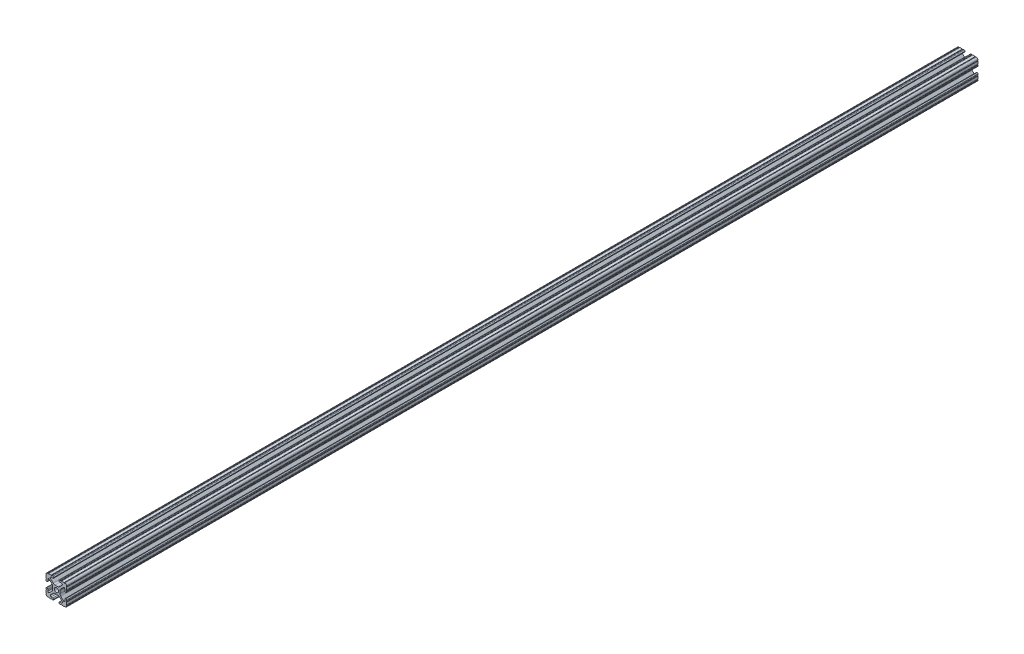
SolidWorks part; units mm, degrees
ref_plane "Front Plane" through (0, 0, 0) normal (0, 0, 1) x (1, 0, 0)
ref_plane "Top Plane" through (0, 0, 0) normal (0, 1, 0) x (1, 0, 0)
ref_plane "Right Plane" through (0, 0, 0) normal (1, 0, 0) x (0, 0, -1)
sketch "Sketch1" plane through (0, 0, 0) normal (0, 0, 1) x (1, 0, 0)
  line L88 (-7.1797, -8.6452) -> (-3.9523, -5.4237)
  line L89 (-1.7093, -4.4958) -> (1.7093, -4.4958)
  line L90 (3.9523, -5.4237) -> (7.1797, -8.6452)
  line L91 (6.4164, -10.4902) -> (4.2875, -10.4902)
  line L92 (3.2385, -11.5392) -> (3.2385, -11.651)
  line L93 (4.2875, -12.7) -> (5.3171, -12.7)
  line L94 (6.3331, -12.7) -> (9.5504, -12.7)
  line L95 (12.7, -9.5504) -> (12.7, -6.3331)
  line L96 (12.7, -5.3171) -> (12.7, -4.2875)
  line L97 (11.651, -3.2385) -> (11.5392, -3.2385)
  line L98 (10.4902, -4.2875) -> (10.4902, -6.4021)
  line L99 (8.7371, -7.1294) -> (5.441, -3.8408)
  line L100 (4.5085, -1.5932) -> (4.5085, 1.5932)
  line L101 (5.441, 3.8408) -> (8.7371, 7.1294)
  line L102 (10.4902, 6.4021) -> (10.4902, 4.2875)
  line L103 (11.5392, 3.2385) -> (11.651, 3.2385)
  line L104 (12.7, 4.2875) -> (12.7, 5.3171)
  line L105 (12.7, 6.3331) -> (12.7, 9.5504)
  line L106 (9.5504, 12.7) -> (6.3331, 12.7)
  line L107 (5.3171, 12.7) -> (4.2875, 12.7)
  line L108 (3.2385, 11.651) -> (3.2385, 11.5392)
  line L109 (4.2875, 10.4902) -> (6.4768, 10.4902)
  line L110 (7.207, 8.7244) -> (3.8983, 5.4232)
  line L111 (1.6558, 4.4958) -> (-1.6558, 4.4958)
  line L112 (-3.8983, 5.4232) -> (-7.207, 8.7244)
  line L113 (-6.4768, 10.4902) -> (-4.2875, 10.4902)
  line L114 (-3.2385, 11.5392) -> (-3.2385, 11.651)
  line L115 (-4.2875, 12.7) -> (-5.3171, 12.7)
  line L116 (-6.3331, 12.7) -> (-9.5504, 12.7)
  line L117 (-12.7, 9.5504) -> (-12.7, 6.3331)
  line L118 (-12.7, 5.3171) -> (-12.7, 4.2875)
  line L119 (-11.651, 3.2385) -> (-11.5392, 3.2385)
  line L120 (-10.4902, 4.2875) -> (-10.4902, 6.4021)
  line L121 (-8.7371, 7.1294) -> (-5.441, 3.8408)
  line L122 (-4.5085, 1.5932) -> (-4.5085, -1.5932)
  line L123 (-5.441, -3.8408) -> (-8.7371, -7.1294)
  line L124 (-10.4902, -6.4021) -> (-10.4902, -4.2875)
  line L125 (-11.5392, -3.2385) -> (-11.651, -3.2385)
  line L126 (-12.7, -4.2875) -> (-12.7, -5.3171)
  line L127 (-12.7, -6.3331) -> (-12.7, -9.5504)
  line L128 (-9.5504, -12.7) -> (-6.3331, -12.7)
  line L129 (-5.3171, -12.7) -> (-4.2875, -12.7)
  line L130 (-3.2385, -11.651) -> (-3.2385, -11.5392)
  line L131 (-4.2875, -10.4902) -> (-6.4164, -10.4902)
  circle A1 centre (0, 0) radius 2.6035
  arc A104 (-7.1797, -8.6452) -> (-6.4164, -10.4902) centre (-6.4164, -9.4098) ccw
  arc A105 (-1.7093, -4.4958) -> (-3.9523, -5.4237) centre (-1.7093, -7.6708) ccw
  arc A106 (3.9523, -5.4237) -> (1.7093, -4.4958) centre (1.7093, -7.6708) ccw
  arc A107 (6.4164, -10.4902) -> (7.1797, -8.6452) centre (6.4164, -9.4098) ccw
  arc A108 (4.2875, -10.4902) -> (3.2385, -11.5392) centre (4.2875, -11.5392) ccw
  arc A109 (3.2385, -11.651) -> (4.2875, -12.7) centre (4.2875, -11.651) ccw
  arc A110 (6.3331, -12.7) -> (5.3171, -12.7) centre (5.8251, -12.7) ccw
  arc A111 (10.5664, -12.6998) -> (9.5504, -12.7) centre (10.0584, -12.7) ccw
  arc A112 (10.5664, -12.6998) -> (12.6998, -10.5664) centre (10.5918, -10.5918) ccw
  arc A113 (12.7, -9.5504) -> (12.6998, -10.5664) centre (12.7, -10.0584) ccw
  arc A114 (12.7, -5.3171) -> (12.7, -6.3331) centre (12.7, -5.8251) ccw
  arc A115 (12.7, -4.2875) -> (11.651, -3.2385) centre (11.651, -4.2875) ccw
  arc A116 (11.5392, -3.2385) -> (10.4902, -4.2875) centre (11.5392, -4.2875) ccw
  arc A117 (8.7371, -7.1294) -> (10.4902, -6.4021) centre (9.4628, -6.4021) ccw
  arc A118 (4.5085, -1.5932) -> (5.441, -3.8408) centre (7.6835, -1.5932) ccw
  arc A119 (5.441, 3.8408) -> (4.5085, 1.5932) centre (7.6835, 1.5932) ccw
  arc A120 (10.4902, 6.4021) -> (8.7371, 7.1294) centre (9.4628, 6.4021) ccw
  arc A121 (10.4902, 4.2875) -> (11.5392, 3.2385) centre (11.5392, 4.2875) ccw
  arc A122 (11.651, 3.2385) -> (12.7, 4.2875) centre (11.651, 4.2875) ccw
  arc A123 (12.7, 6.3331) -> (12.7, 5.3171) centre (12.7, 5.8251) ccw
  arc A124 (12.6998, 10.5664) -> (12.7, 9.5504) centre (12.7, 10.0584) ccw
  arc A125 (12.6998, 10.5664) -> (10.5664, 12.6998) centre (10.5918, 10.5918) ccw
  arc A126 (9.5504, 12.7) -> (10.5664, 12.6998) centre (10.0584, 12.7) ccw
  arc A127 (5.3171, 12.7) -> (6.3331, 12.7) centre (5.8251, 12.7) ccw
  arc A128 (4.2875, 12.7) -> (3.2385, 11.651) centre (4.2875, 11.651) ccw
  arc A129 (3.2385, 11.5392) -> (4.2875, 10.4902) centre (4.2875, 11.5392) ccw
  arc A130 (7.207, 8.7244) -> (6.4768, 10.4902) centre (6.4768, 9.4563) ccw
  arc A131 (1.6558, 4.4958) -> (3.8983, 5.4232) centre (1.6558, 7.6708) ccw
  arc A132 (-3.8983, 5.4232) -> (-1.6558, 4.4958) centre (-1.6558, 7.6708) ccw
  arc A133 (-6.4768, 10.4902) -> (-7.207, 8.7244) centre (-6.4768, 9.4563) ccw
  arc A134 (-4.2875, 10.4902) -> (-3.2385, 11.5392) centre (-4.2875, 11.5392) ccw
  arc A135 (-3.2385, 11.651) -> (-4.2875, 12.7) centre (-4.2875, 11.651) ccw
  arc A136 (-6.3331, 12.7) -> (-5.3171, 12.7) centre (-5.8251, 12.7) ccw
  arc A137 (-10.5664, 12.6998) -> (-9.5504, 12.7) centre (-10.0584, 12.7) ccw
  arc A138 (-10.5664, 12.6998) -> (-12.6998, 10.5664) centre (-10.5918, 10.5918) ccw
  arc A139 (-12.7, 9.5504) -> (-12.6998, 10.5664) centre (-12.7, 10.0584) ccw
  arc A140 (-12.7, 5.3171) -> (-12.7, 6.3331) centre (-12.7, 5.8251) ccw
  arc A141 (-12.7, 4.2875) -> (-11.651, 3.2385) centre (-11.651, 4.2875) ccw
  arc A142 (-11.5392, 3.2385) -> (-10.4902, 4.2875) centre (-11.5392, 4.2875) ccw
  arc A143 (-8.7371, 7.1294) -> (-10.4902, 6.4021) centre (-9.4628, 6.4021) ccw
  arc A144 (-4.5085, 1.5932) -> (-5.441, 3.8408) centre (-7.6835, 1.5932) ccw
  arc A145 (-5.441, -3.8408) -> (-4.5085, -1.5932) centre (-7.6835, -1.5932) ccw
  arc A146 (-10.4902, -6.4021) -> (-8.7371, -7.1294) centre (-9.4628, -6.4021) ccw
  arc A147 (-10.4902, -4.2875) -> (-11.5392, -3.2385) centre (-11.5392, -4.2875) ccw
  arc A148 (-11.651, -3.2385) -> (-12.7, -4.2875) centre (-11.651, -4.2875) ccw
  arc A149 (-12.7, -6.3331) -> (-12.7, -5.3171) centre (-12.7, -5.8251) ccw
  arc A150 (-12.6998, -10.5664) -> (-12.7, -9.5504) centre (-12.7, -10.0584) ccw
  arc A151 (-12.6998, -10.5664) -> (-10.5664, -12.6998) centre (-10.5918, -10.5918) ccw
  arc A152 (-9.5504, -12.7) -> (-10.5664, -12.6998) centre (-10.0584, -12.7) ccw
  arc A153 (-5.3171, -12.7) -> (-6.3331, -12.7) centre (-5.8251, -12.7) ccw
  arc A154 (-4.2875, -12.7) -> (-3.2385, -11.651) centre (-4.2875, -11.651) ccw
  arc A155 (-3.2385, -11.5392) -> (-4.2875, -10.4902) centre (-4.2875, -11.5392) ccw
extrude "Boss-Extrude1" add sketch "Sketch1" along normal mid plane 1117.6
